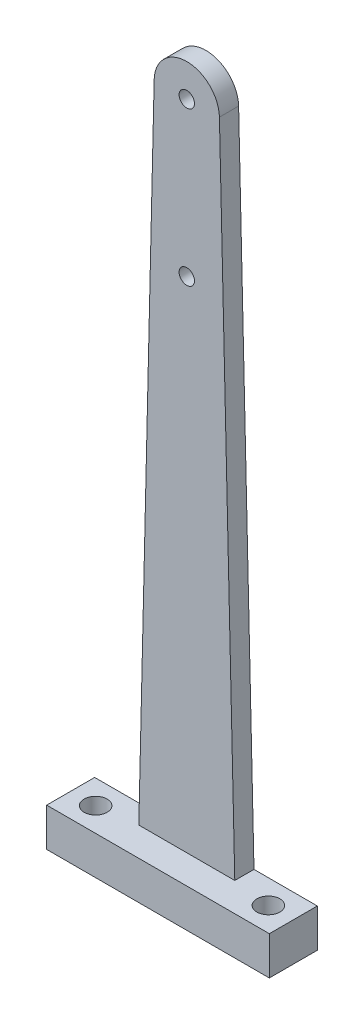
SolidWorks part; units mm, degrees
ref_plane "Front Plane" through (0, 0, 0) normal (0, 0, 1) x (1, 0, 0)
ref_plane "Top Plane" through (0, 0, 0) normal (0, 1, 0) x (1, 0, 0)
ref_plane "Right Plane" through (0, 0, 0) normal (1, 0, 0) x (0, 0, -1)
sketch "Sketch1" plane through (0, 0, 0) normal (0, 0, 1) x (1, 0, 0)
  line L0 (-75.4977, -127.1541) -> (-58.5023, -127.1541) construction
  line L2 (-75.4977, -127.1541) -> (-79.5, -297.3539)
  line L3 (-58.5023, -127.1541) -> (-54.5, -297.3539)
  line L5 (-79.5, -297.3539) -> (-54.5, -297.3539) construction
  line L6 (-67, -127.3539) -> (-67, -297.3539) construction
  line L7 (-96, -297.3539) -> (-79.5, -297.3539)
  line L8 (-96, -297.3539) -> (-96, -307.3539)
  line L9 (-96, -307.3539) -> (-38, -307.3539)
  line L10 (-38, -297.3539) -> (-38, -307.3539)
  line L11 (-67, -307.3539) -> (-67, -297.3539) construction
  line L12 (-54.5, -297.3539) -> (-38, -297.3539)
  circle A0 centre (-67, -167.3539) radius 2 construction
  circle A1 centre (-67, -127.3539) radius 2 construction
  circle A2 centre (-67, -167.3539) radius 2
  circle A3 centre (-67, -127.3539) radius 2
  arc A4 (-75.4977, -127.1541) -> (-58.5023, -127.1541) centre (-67, -127.3539) cw
  dimension "D5" = 8.5
  dimension "D1" = 170
  dimension "D2" = 58
  dimension "D3" = 10
  dimension "D4" = 25
extrude "Boss-Extrude1" add sketch "Sketch1" along normal blind 5
ref_plane "Plane1" through (0, 0, 2.5) normal (0, 0, 1) x (1, 0, 0)
sketch "Sketch2" plane through (0, 0, 2.5) normal (0, 0, 1) x (1, 0, 0)
  line L0 (-96, -297.3539) -> (-96, -307.3539) construction
  line L2 (-38, -297.3539) -> (-54.5, -297.3539) construction
  line L3 (-38, -307.3539) -> (-38, -297.3539) construction
  line L4 (-96, -307.3539) -> (-38, -307.3539) construction
  line L5 (-96, -297.3539) -> (-96, -307.3539)
  line L7 (-38, -297.3539) -> (-96, -297.3539)
  line L8 (-38, -307.3539) -> (-38, -297.3539)
  line L9 (-96, -307.3539) -> (-38, -307.3539)
extrude "Boss-Extrude2" add sketch "Sketch2" along normal blind 10
sketch "Sketch3" plane through (0, -297.3539, 0) normal (0, 1, 0) x (1, 0, 0)
  line L0 (-89.5, -6.25) -> (-44.5, -6.25) construction
  line L1 (-96, -12.5) -> (-96, 0) construction
  line L2 (-67, -12.5) -> (-67, 0) construction
  line L3 (-38, -12.5) -> (-96, -12.5) construction
  circle A0 centre (-89.5, -6.25) radius 3
  circle A1 centre (-44.5, -6.25) radius 3
  point P7 (-96, -6.25)
  point P11 (-67, -6.25)
  dimension "D2" = 6
  dimension "D1" = 45
extrude "Cut-Extrude1" cut sketch "Sketch3" against normal through all
